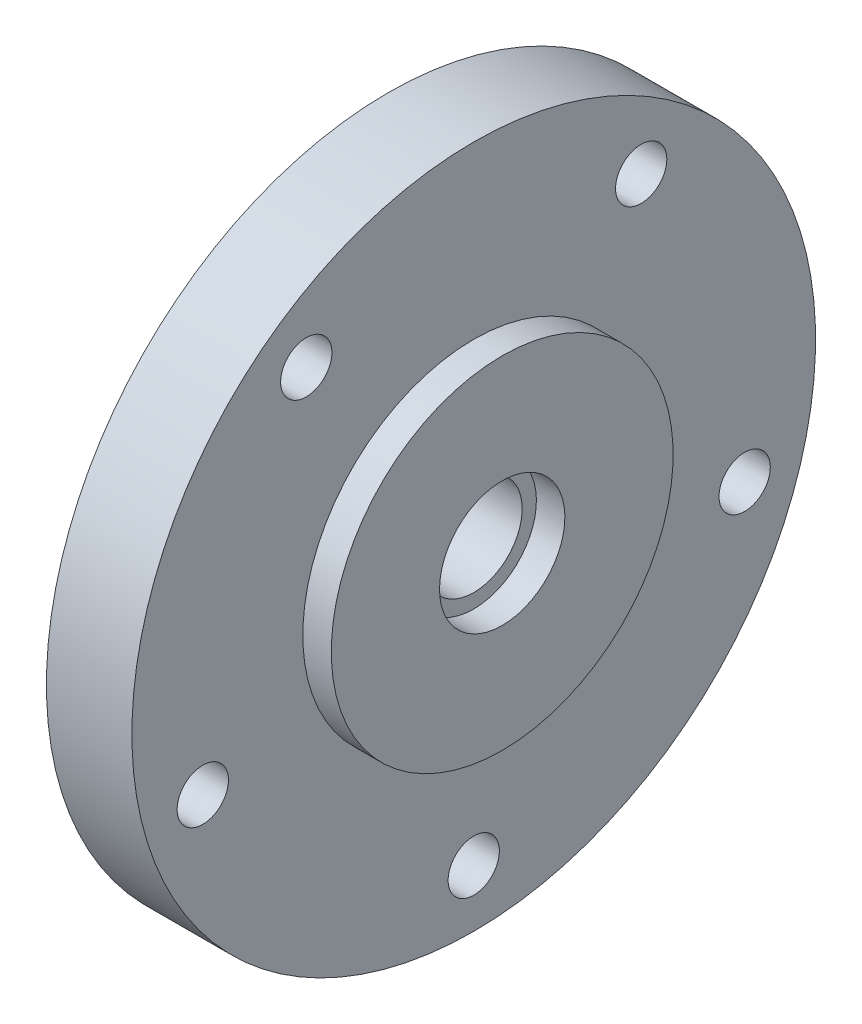
SolidWorks part; units mm, degrees
material "1.0037 (S235JR)"
ref_plane "Front Plane" through (0, 0, 0) normal (0, 0, 1) x (1, 0, 0)
ref_plane "Top Plane" through (0, 0, 0) normal (0, 1, 0) x (1, 0, 0)
ref_plane "Right Plane" through (0, 0, 0) normal (1, 0, 0) x (0, 0, -1)
sketch "Sketch2" plane through (0, 0, 0) normal (0, 0, 1) x (1, 0, 0)
  line L0 (-20, 0) -> (0, 0) construction
  line L1 (0, 0) -> (0, 30)
  line L2 (0, 30) -> (-5, 30)
  line L3 (-5, 30) -> (-5, 60)
  line L4 (-20, 12.5) -> (-10, 12.5)
  line L5 (-20, 12.5) -> (-20, 0)
  line L6 (-20, 8.5) -> (-5, 8.5)
  line L7 (-10, 12.5) -> (-10, 40)
  line L8 (-10, 40) -> (-20, 40)
  line L9 (-20, 40) -> (-20, 60)
  line L10 (-20, 60) -> (-5, 60)
  line L11 (-5, 8.5) -> (-5, 11)
  line L12 (-5, 11) -> (0, 11)
  dimension "D1" = 25
  dimension "D2" = 17
  dimension "D4" = 80
  dimension "D5" = 60
  dimension "120" = 120
  dimension "D6" = 10
  dimension "D7" = 5
  dimension "D8" = 5
  dimension "D9" = 5
  dimension "D10" = 22
revolve "Revolve1" add sketch "Sketch2" angle 360 about L0
sketch "Sketch3" plane through (-5, 0, 0) normal (1, 0, 0) x (0, 0, -1)
  point P0 (0, -50)
  dimension "D1" = 50
hole_wizard "M8 Clearance Hole1" positions "3DSketch1" profile "Sketch4" hole size "M8" standard "ISO" end condition up to next
sketch3d "3DSketch1"
  point P0 (-5, -50, 0)
sketch "Sketch4" plane through (-5, -50, 0) normal (0, 1, 0) x (0, 0, -1)
  line L0 (0, 0) -> (0, 15)
  line L1 (0, 15) -> (4.5, 15)
  line L2 (4.5, 15) -> (4.5, 0)
  line L5 (4.5, 0) -> (0, 0)
  line L11 (0, -6.35) -> (0, 107.95) construction
  dimension "Thru Hole Dia." = 9
  dimension "Thru Hole Depth" = 15
pattern_circular "CirPattern1" count 5 over 360 about axis through (0, 0, 0) along (1, 0, 0) of "M8 Clearance Hole1"
